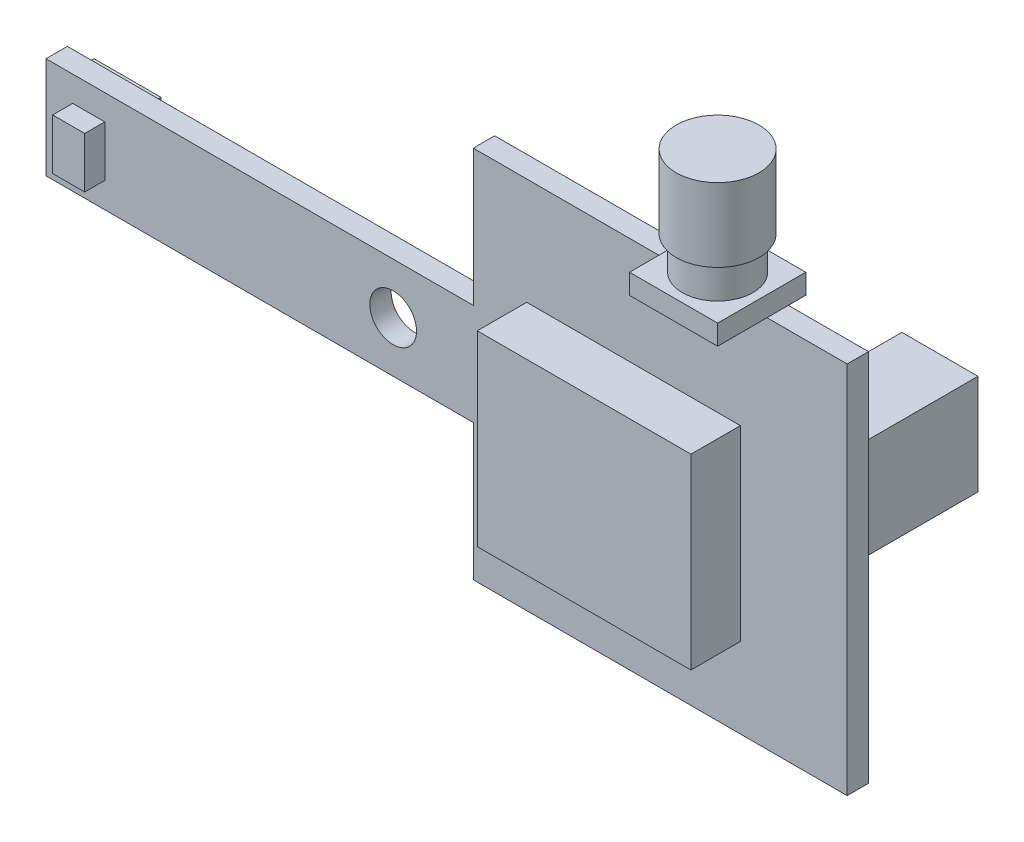
SolidWorks part; units mm, degrees
ref_plane "Front Plane" through (0, 0, 0) normal (0, 0, 1) x (1, 0, 0)
ref_plane "Top Plane" through (0, 0, 0) normal (0, 1, 0) x (1, 0, 0)
ref_plane "Right Plane" through (0, 0, 0) normal (1, 0, 0) x (0, 0, -1)
sketch "Sketch1" plane through (0, 0, 0) normal (0, 0, 1) x (1, 0, 0)
  line L0 (0, 0) -> (-6, 0) construction
  line L1 (0, 14) -> (28, 14)
  line L2 (0, 14) -> (0, -14)
  line L3 (0, -14) -> (28, -14)
  line L4 (28, 14) -> (28, -14)
  line L5 (-32, 3.8) -> (0, 3.8)
  line L6 (-32, 3.8) -> (-32, -3.8)
  line L7 (-32, -3.8) -> (0, -3.8)
  line L8 (0, 3.8) -> (0, -3.8)
  circle A0 centre (-6, 0) radius 1.75
  point P4 (0, 0)
  point P10 (0, 0)
  dimension "D5" = 3.5
  dimension "D1" = 28
  dimension "D2" = 28
  dimension "D3" = 7.6
  dimension "D4" = 60
  dimension "D6" = 26
  dimension "D7" = 34
extrude "Boss-Extrude1" add sketch "Sketch1" along normal blind 1.6
sketch "Sketch2" plane through (0, 14, 0) normal (0, 1, 0) x (1, 0, 0)
  line L0 (28, -1.6) -> (28, 0) construction
  line L1 (15.4, 1.3) -> (22, 1.3)
  line L2 (15.4, 1.3) -> (15.4, -5.3)
  line L3 (15.4, -5.3) -> (22, -5.3)
  line L4 (22, 1.3) -> (22, -5.3)
  line L5 (0, -1.6) -> (0, 0) construction
  line L6 (0, -1.6) -> (28, -1.6) construction
  line L8 (0, 0) -> (28, 0) construction
  point P6 (28, -0.8)
  dimension "D1" = 6.6
  dimension "D2" = 6.6
  dimension "D3" = 6
  dimension "D4" = 15.4
  dimension "D5" = 2.9
  dimension "D6" = 5.3
extrude "Boss-Extrude2" add sketch "Sketch2" along normal blind 1.5 separate body
sketch "Sketch3" plane through (0, 15.5, 0) normal (0, 1, 0) x (1, 0, 0)
  line L0 (15.4, 1.3) -> (22, -5.3) construction
  circle A0 centre (18.7, -2) radius 2.65
  dimension "D1" = 5.3
extrude "Boss-Extrude3" add sketch "Sketch3" along normal blind 2.5
sketch "Sketch4" plane through (0, 18, 0) normal (0, 1, 0) x (1, 0, 0)
  circle A0 centre (18.7, -2) radius 3.1
  dimension "D1" = 6.2
extrude "Boss-Extrude4" add sketch "Sketch4" along normal blind 5.5
sketch "Sketch5" plane through (0, 0, 1.6) normal (0, 0, 1) x (1, 0, 0)
  line L0 (0, -14) -> (28, -14) construction
  line L1 (4, 6) -> (20, 6)
  line L2 (4, 6) -> (4, -8)
  line L3 (4, -8) -> (20, -8)
  line L4 (20, 6) -> (20, -8)
  line L5 (0, 14) -> (28, 14) construction
  line L6 (0, -3.8) -> (0, -14) construction
  line L7 (28, 14) -> (28, -14) construction
  dimension "D1" = 16
  dimension "D2" = 14
  dimension "D3" = 20
  dimension "D4" = 22
  dimension "D5" = 20
  dimension "D6" = 24
extrude "Boss-Extrude5" add sketch "Sketch5" along normal up to surface (3.7 mm away) separate body up to face at (18.7, 14.75, 5.3)
sketch "Sketch6" plane through (0, 0, 1.6) normal (0, 0, 1) x (1, 0, 0)
  line L0 (-32, 3.8) -> (0, 3.8) construction
  line L1 (-30, 1.9) -> (-27.6, 1.9)
  line L2 (-30, 1.9) -> (-30, -1.9)
  line L3 (-30, -1.9) -> (-27.6, -1.9)
  line L4 (-27.6, 1.9) -> (-27.6, -1.9)
  line L5 (-32, -3.8) -> (0, -3.8) construction
  line L6 (-32, 3.8) -> (-32, -3.8) construction
  line L7 (28, 14) -> (28, -14) construction
  dimension "D1" = 2.4
  dimension "D2" = 3.8
  dimension "D3" = 5.7
  dimension "D4" = 5.7
  dimension "D5" = 4.4
  dimension "D6" = 58
extrude "Boss-Extrude6" add sketch "Sketch6" along normal blind 1.5 separate body
sketch "Sketch7" plane through (0, 0, 0) normal (0, 0, -1) x (-1, 0, 0)
  line L0 (32, 3.8) -> (32, -3.8) construction
  line L1 (-26.7, 7) -> (-21, 7)
  line L2 (-26.7, 7) -> (-26.7, -0.5)
  line L3 (-26.7, -0.5) -> (-21, -0.5)
  line L4 (-21, 7) -> (-21, -0.5)
  line L5 (-12.7, 2.8) -> (-5.4, 2.8)
  line L6 (-12.7, 2.8) -> (-12.7, -4)
  line L7 (-12.7, -4) -> (-5.4, -4)
  line L8 (-5.4, 2.8) -> (-5.4, -4)
  line L9 (26.5, 2.5) -> (31.5, 2.5)
  line L10 (26.5, 2.5) -> (26.5, -2.5)
  line L11 (26.5, -2.5) -> (31.5, -2.5)
  line L12 (31.5, 2.5) -> (31.5, -2.5)
  line L13 (32, 3.8) -> (0, 3.8) construction
  line L14 (32, -3.8) -> (0, -3.8) construction
  line L15 (0, 14) -> (-28, 14) construction
  line L16 (0, -14) -> (-28, -14) construction
  line L17 (-28, 14) -> (-28, -14) construction
  line L18 (0, -3.8) -> (0, -14) construction
  dimension "D1" = 5
  dimension "D2" = 5
  dimension "D3" = 5.5
  dimension "D4" = 6.3
  dimension "D5" = 6.3
  dimension "D6" = 7.3
  dimension "D7" = 6.8
  dimension "D8" = 18
  dimension "D9" = 16.8
  dimension "D10" = 22.6
  dimension "D11" = 12.7
  dimension "D12" = 5.7
  dimension "D13" = 7.5
  dimension "D14" = 7
  dimension "D15" = 21
  dimension "D16" = 14.5
extrude "Boss-Extrude7" add sketch "Sketch7" along normal blind 1.5 separate body
other "Move Face2" face at (23.85, 3.25, -1.5) parameters "D1"=8
